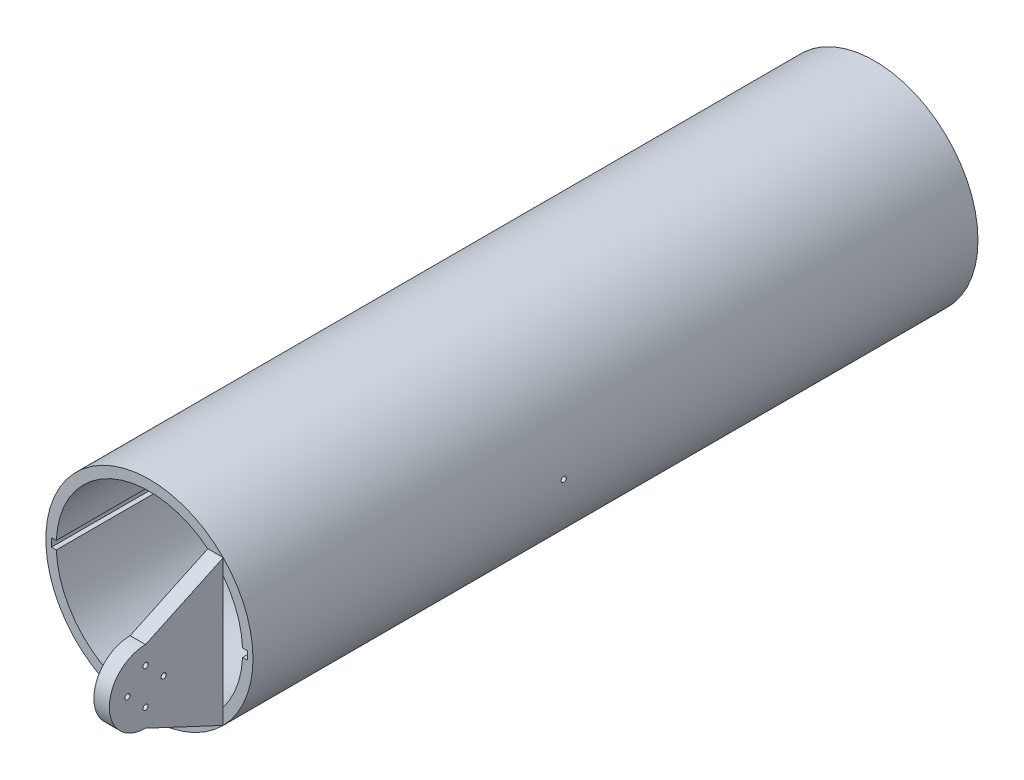
SolidWorks part; units mm, degrees
ref_plane "Front Plane" through (0, 0, 0) normal (0, 0, 1) x (1, 0, 0)
ref_plane "Top Plane" through (0, 0, 0) normal (0, 1, 0) x (1, 0, 0)
ref_plane "Right Plane" through (0, 0, 0) normal (1, 0, 0) x (0, 0, -1)
sketch "Sketch1" plane through (0, 0, 0) normal (0, 0, 1) x (1, 0, 0)
  line L0 (0, 45) -> (0, -22.6804) construction
  line L1 (-44.9556, 1.9995) -> (-47.2556, 1.9995)
  line L2 (-47.2556, 1.9995) -> (-47.2556, -1.9995)
  line L3 (44.9556, -1.9995) -> (47.2556, -1.9995)
  line L4 (-44.9556, -1.9995) -> (-47.2556, -1.9995)
  line L5 (47.2556, 1.9995) -> (47.2556, -1.9995)
  line L6 (44.9556, 1.9995) -> (47.2556, 1.9995)
  circle A0 centre (0, 0) radius 50
  arc A1 (-44.9556, -1.9995) -> (44.9556, -1.9995) centre (0, 0) ccw
  arc A2 (44.9556, 1.9995) -> (-44.9556, 1.9995) centre (0, 0) ccw
extrude "Boss-Extrude1" add sketch "Sketch1" along normal blind 250 and the other way blind 100
sketch "Sketch3" plane through (0, 0, 250) normal (0, 0, 1) x (1, 0, 0)
  line L0 (0, 0) -> (28.2, 0) construction
  line L1 (28.2, 0) -> (28.2, 35.0679)
  line L2 (28.2, 35.0679) -> (35.6404, 35.0679)
  line L3 (35.6404, 35.0679) -> (35.6404, -35.0679)
  line L4 (35.6404, -35.0679) -> (28.2, -35.0679)
  line L5 (28.2, -35.0679) -> (28.2, 0)
  arc A0 (44.9556, 1.9995) -> (-44.9556, 1.9995) centre (0, 0) ccw construction
  circle A1 centre (0, 0) radius 50 construction
  arc A2 (-44.9556, -1.9995) -> (44.9556, -1.9995) centre (0, 0) ccw construction
extrude "Boss-Extrude2" add sketch "Sketch3" along normal blind 55
sketch "Sketch7" plane through (35.6404, 0, 0) normal (1, 0, 0) x (0, 0, -1)
  line L0 (-250, 0) -> (-100, 0) construction
  line L1 (-250, -27.4729) -> (-250, 27.4729) construction
  circle A0 centre (-100, 0) radius 1.25
extrude "Cut-Extrude4" cut sketch "Sketch7" against normal blind 96 and the other way blind 75
sketch "Sketch8" plane through (35.6404, 0, 0) normal (1, 0, 0) x (0, 0, -1)
  line L0 (-305, 0) -> (-287.5, 0) construction
  line L1 (-305, -35.0679) -> (-305, 35.0679) construction
  line L2 (-287.5, 0) -> (-270, 0) construction
  line L3 (-287.5, 17.5) -> (-250, 35.0679)
  line L4 (-250, 35.0679) -> (-305, 35.0679)
  line L5 (-305, 35.0679) -> (-305, 0)
  arc A0 (-287.5, 17.5) -> (-305, 0) centre (-287.5, 0) ccw
extrude "Cut-Extrude5" cut sketch "Sketch8" against normal blind 96
sketch "Sketch9" plane through (35.6404, 0, 0) normal (1, 0, 0) x (0, 0, -1)
  line L0 (-287.5, -17.5) -> (-250, -35.0679)
  line L1 (-250, -35.0679) -> (-305, -35.0679)
  line L2 (-305, -35.0679) -> (-305, 0)
  arc A0 (-305, 0) -> (-287.5, -17.5) centre (-287.5, 0) ccw
extrude "Cut-Extrude6" cut sketch "Sketch9" against normal blind 96
sketch "Sketch10" plane through (35.6404, 0, 0) normal (1, 0, 0) x (0, 0, -1)
  line L0 (-287.5, 17.5) -> (-287.5, 0) construction
  line L1 (-287.5, 0) -> (-287.5, -17.5) construction
  line L2 (-305, 0) -> (-287.5, 0) construction
  line L3 (-287.5, 0) -> (-270, 0) construction
  arc A0 (-287.5, 17.5) -> (-287.5, -17.5) centre (-287.5, 0) ccw construction
  circle A1 centre (-296.25, 0) radius 1.25
  circle A2 centre (-287.5, 8.75) radius 1.25
  circle A3 centre (-278.75, 0) radius 1.25
  circle A4 centre (-287.5, -8.75) radius 1.25
extrude "Cut-Extrude7" cut sketch "Sketch10" against normal blind 96
